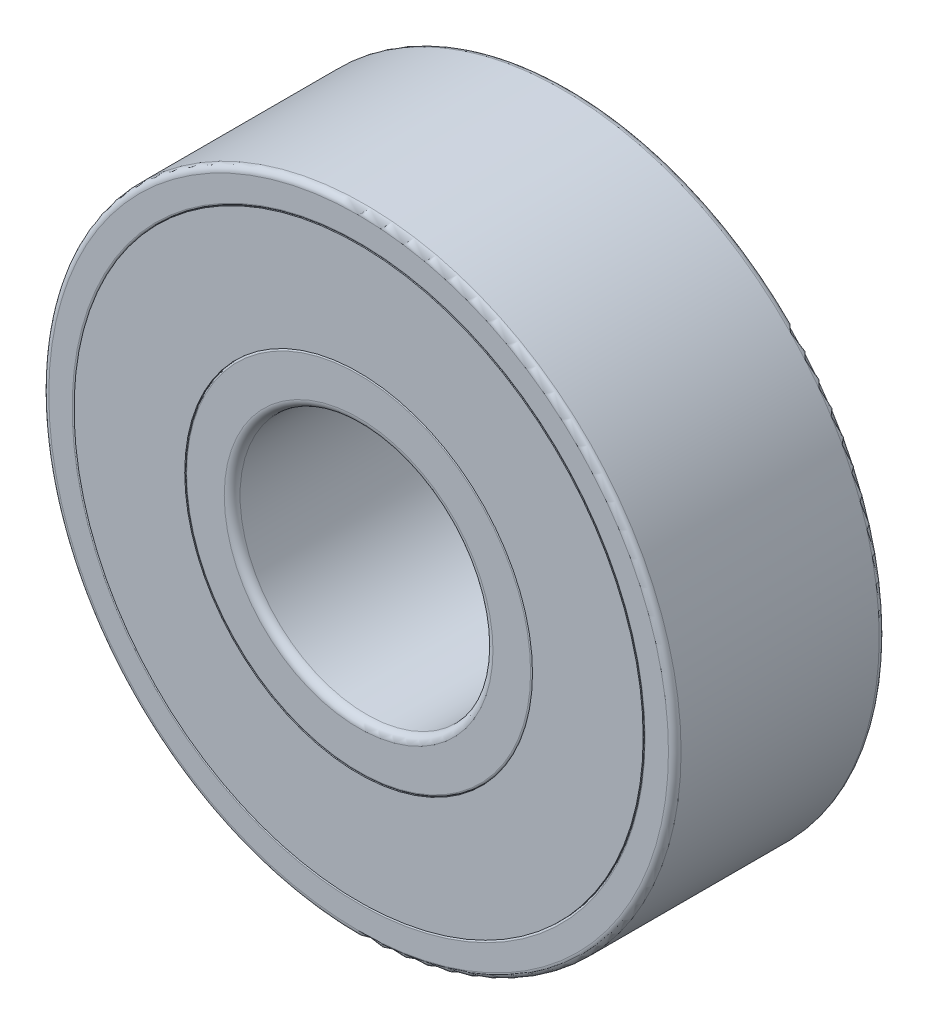
SolidWorks part; units mm, degrees
ref_plane "Front Plane" through (0, 0, 0) normal (0, 0, 1) x (1, 0, 0)
ref_plane "Top Plane" through (0, 0, 0) normal (0, 1, 0) x (1, 0, 0)
ref_plane "Right Plane" through (0, 0, 0) normal (1, 0, 0) x (0, 0, -1)
sketch "Sketch1" plane through (0, 0, 0) normal (0, 0, 1) x (1, 0, 0)
  line L0 (0, 7.5) -> (0, 5.25) construction
  line L1 (0, 5.25) -> (0, 3) construction
  line L2 (0, 7.5) -> (0, 6.75) construction
  line L3 (0, 6.75) -> (0, 6) construction
  line L4 (0, 6) -> (0, 5.25) construction
  circle A0 centre (0, 0) radius 3
  circle A1 centre (0, 0) radius 7.5
  circle A2 centre (0, 0) radius 6.75 construction
  circle A4 centre (0, 0) radius 4.125 construction
  point P5 (0, 4.125)
  dimension "OD" = 15
  dimension "ID" = 6
sketch "Sketch2" plane through (0, 0, 0) normal (1, 0, 0) x (0, 0, -1)
  line L0 (-2.5, -7.5) -> (2.5, -7.5) construction
  point P2 (0, -7.5)
  dimension "Width" = 5
sketch "Sketch3" plane through (0, 0, 0) normal (1, 0, 0) x (0, 0, -1)
  line L0 (-2.5, -7.5) -> (2.5, -7.5)
  line L1 (2.5, -7.5) -> (2.5, -6.75)
  line L2 (2.5, -6.75) -> (-2.5, -6.75)
  line L3 (-2.5, -6.75) -> (-2.5, -7.5)
  line L6 (-2.5, -3) -> (2.5, -3)
  line L9 (-2.5, -4.125) -> (2.5, -4.125)
  line L12 (-2.5, -4.125) -> (-2.5, -3)
  line L13 (2.5, -4.125) -> (2.5, -3)
  line L14 (-2.5, 0) -> (2.5, 0) construction
  point P6 (0, -6.75)
  point P7 (0, -4.125)
  point P8 (0, -3)
  dimension "D1" = 2.625
revolve "Revolve1" add sketch "Sketch3" angle 360 about L14
sketch "Sketch4" plane through (0, 0, 0) normal (1, 0, 0) x (0, 0, -1)
  line L0 (0, 7.5) -> (0, -7.5) construction
  line L1 (-2.5, -4.125) -> (-2.5, -6.75) construction
  circle A0 centre (0, -5.4375) radius 1.575
  point P8 (-2.5, -5.4375)
  dimension "D1" = 3.15
revolve "Cut-Revolve1" cut sketch "Sketch4" angle 360 about L14
sketch "Sketch5" plane through (0, 0, 0) normal (1, 0, 0) x (0, 0, -1)
  line L0 (0, -3.8625) -> (0, -7.0125)
  line L1 (0, 7.5) -> (0, -7.5) construction
  circle A0 centre (0, -5.4375) radius 1.575 construction
  arc A1 (0, -3.8625) -> (0, -7.0125) centre (0, -5.4375) cw
revolve "Revolve2" add sketch "Sketch5" angle 360 about L0
pattern_circular "CirPattern1" count 7 over 360 about axis through (0, 0, 0) along (0, 0, 1) of bodies 138
fillet "Fillet1" radius 0.15 2 edges at (7.5, 0, -2.5) (7.5, 0, 2.5)
fillet "Fillet2" radius 0.1875 2 edges at (3, 0, -2.5) (3, 0, 2.5)
fillet "Fillet3" radius 0.045 2 edges at (6.75, 0, -2.5) (6.75, 0, 2.5)
fillet "Fillet4" radius 0.045 2 edges at (4.125, 0, -2.5) (4.125, 0, 2.5)
sketch "Sketch6" plane through (0, 0, 0) normal (0, 0, 1) x (1, 0, 0)
  circle A0 centre (0, 0) radius 6.75 construction
  circle A1 centre (0, 0) radius 6.75
  circle A2 centre (0, 0) radius 4.125 construction
  circle A3 centre (0, 0) radius 4.125
extrude "Boss-Extrude2" add sketch "Sketch6" along normal mid plane 5 separate body
equation "\"D1@Sketch4\"=\"D1@Sketch3\"*1.2"
equation "\"D1@Fillet1\"=\"OD@Sketch1\"*0.01"
equation "\"D1@Fillet2\"=\"D1@Fillet1\"*1.25"
equation "\"D1@Fillet3\"=\"D1@Fillet1\"*0.3"
equation "\"D1@Fillet4\"=\"D1@Fillet3\""
equation "\"D1@Boss-Extrude2\"=\"width@sketch2\""
